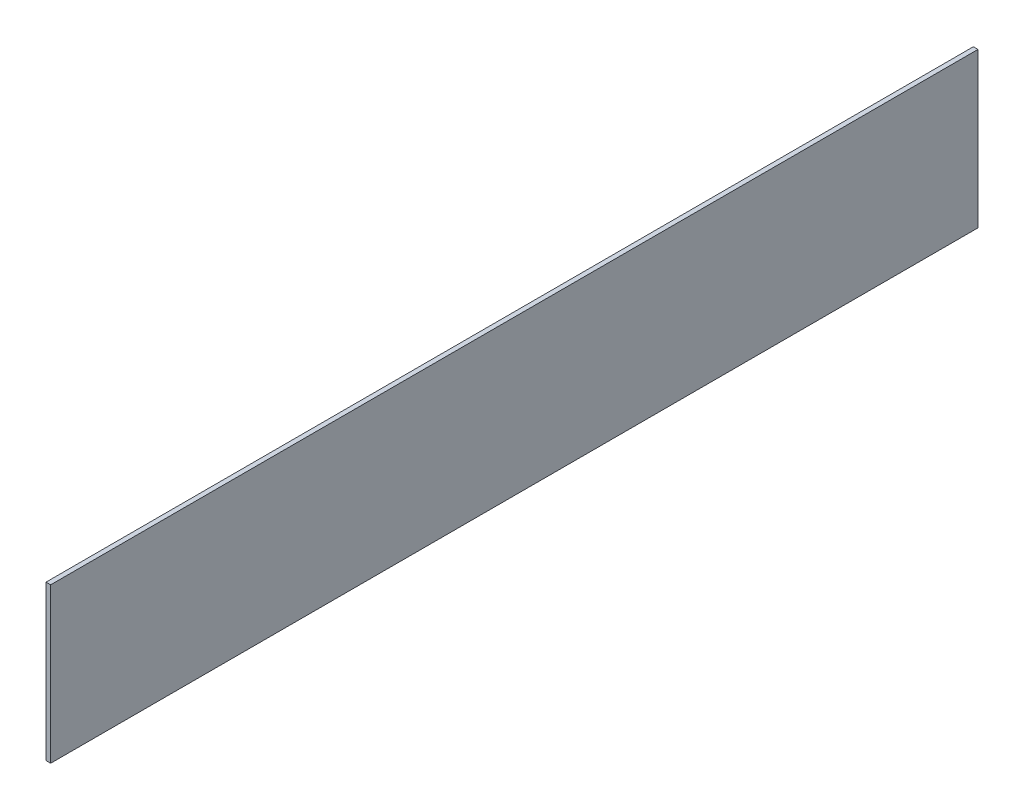
SolidWorks part; units mm, degrees
ref_plane "Front Plane" through (0, 0, 0) normal (0, 0, 1) x (1, 0, 0)
ref_plane "Top Plane" through (0, 0, 0) normal (0, 1, 0) x (1, 0, 0)
ref_plane "Right Plane" through (0, 0, 0) normal (1, 0, 0) x (0, 0, -1)
sketch "Sketch1" plane through (1495.226, 0, 0) normal (1, 0, 0) x (0, 0, -1)
  line L1 (23.5462, 0) -> (-576.4538, 0)
  line L2 (23.5462, 0) -> (23.5462, 100)
  line L3 (23.5462, 100) -> (-576.4538, 100)
  line L4 (-576.4538, 0) -> (-576.4538, 100)
  dimension "D1" = 100
  dimension "D2" = 600
extrude "Boss-Extrude1" add sketch "Sketch1" along normal blind 3
